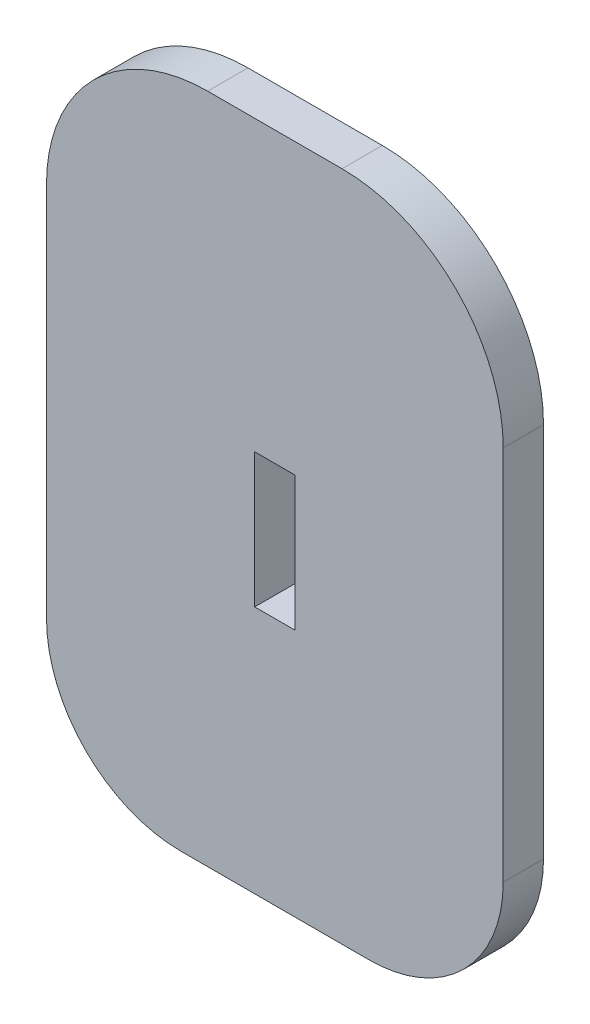
SolidWorks part; units mm, degrees
ref_plane "Front Plane" through (0, 0, 0) normal (0, 0, 1) x (1, 0, 0)
ref_plane "Top Plane" through (0, 0, 0) normal (0, 1, 0) x (1, 0, 0)
ref_plane "Right Plane" through (0, 0, 0) normal (1, 0, 0) x (0, 0, -1)
sketch "Sketch1" plane through (0, 0, 0) normal (0, 0, 1) x (1, 0, 0)
  line L0 (0, -21.5) -> (0, -71.5) construction
  line L1 (-17, -21.5) -> (17, -21.5) construction
  line L2 (-17, -21.5) -> (-17, -71.5) construction
  line L3 (-17, -71.5) -> (17, -71.5) construction
  line L4 (17, -21.5) -> (17, -71.5) construction
  line L5 (-5, -21.5) -> (5, -21.5)
  line L6 (-7, -71.5) -> (7, -71.5) construction
  line L7 (-17, -33.5) -> (17, -33.5) construction
  line L8 (-17, -33.5) -> (-17, -61.5)
  line L9 (-17, -61.5) -> (17, -61.5) construction
  line L10 (17, -33.5) -> (17, -61.5)
  line L11 (-0.5, -71.5) -> (0.5, -71.5) construction
  line L12 (-7, -71.5) -> (-0.5, -71.5)
  line L13 (0.5, -71.5) -> (7, -71.5)
  line L14 (-0.5, -71.5) -> (0.5, -71.5)
  arc A0 (-17, -33.5) -> (-5, -21.5) centre (-5, -33.5) cw
  arc A1 (5, -21.5) -> (17, -33.5) centre (5, -33.5) cw
  arc A2 (-17, -61.5) -> (-7, -71.5) centre (-7, -61.5) ccw
  arc A3 (7, -71.5) -> (17, -61.5) centre (7, -61.5) ccw
  point P10 (0, -21.5)
  point P19 (0, -71.5)
  point P23 (0, -71.5)
  dimension "D3" = 12
  dimension "D4" = 10
  dimension "D1" = 50
  dimension "D2" = 34
  dimension "D5" = 1
  dimension "D6" = 21.5
extrude "Boss-Extrude1" add sketch "Sketch1" along normal blind 3
sketch "Sketch2" plane through (0, 0, 3) normal (0, 0, 1) x (1, 0, 0)
  line L0 (0, -1.65) -> (0, 1.65) construction
  line L1 (-1.5, -53) -> (1.5, -53)
  line L2 (-1.5, -53) -> (-1.5, -43)
  line L3 (-1.5, -43) -> (1.5, -43)
  line L4 (1.5, -53) -> (1.5, -43)
  line L5 (-1.5, -53) -> (1.5, -43) construction
  line L6 (-1.5, -43) -> (1.5, -53) construction
  line L7 (-7, -71.5) -> (7, -71.5) construction
  point P0 (0, -48)
  dimension "D1" = 10
  dimension "D2" = 3
  dimension "D3" = 18.5
extrude "Cut-Extrude1" cut sketch "Sketch2" against normal blind 10
